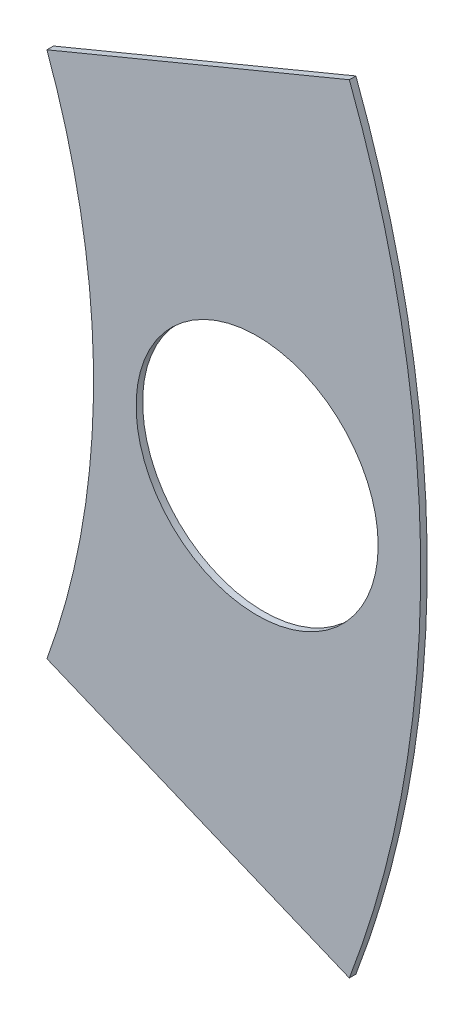
SolidWorks part; units mm, degrees
material "Copper"
ref_plane "Front Plane" through (0, 0, 0) normal (0, 0, 1) x (1, 0, 0)
ref_plane "Top Plane" through (0, 0, 0) normal (0, 1, 0) x (1, 0, 0)
ref_plane "Right Plane" through (0, 0, 0) normal (1, 0, 0) x (0, 0, -1)
sketch "Sketch4" plane through (0, 0, 0) normal (0, 0, 1) x (1, 0, 0)
  circle A0 centre (0, 0) radius 42.545
  dimension "D1" = 85.09
extrude "Boss-Extrude2" add sketch "Sketch4" along normal blind 0.254
sketch "Sketch5" plane through (0, 0, 0.254) normal (0, 0, 1) x (1, 0, 0)
  circle A0 centre (0, 0) radius 29.845
  circle A1 centre (0, 0) radius 42.545 construction
  dimension "D1" = 12.7
extrude "Cut-Extrude5" cut sketch "Sketch5" against normal through all
sketch "Sketch6" plane through (0, 0, 0.254) normal (0, 0, 1) x (1, 0, 0)
  line L0 (0, 0) -> (36.195, 0) construction
  circle A0 centre (36.195, 0) radius 4.699
  circle A1 centre (0, 0) radius 29.845 construction
  dimension "D2" = 9.398
  dimension "D1" = 6.35
extrude "Cut-Extrude6" cut sketch "Sketch6" against normal through all
sketch "Sketch8" plane through (0, 0, 0.254) normal (0, 0, 1) x (1, 0, 0)
  line L0 (0, 0) -> (39.3065, 16.2813) construction
  line L1 (0, 0) -> (39.3065, -16.2813) construction
  line L2 (28.0342, -10.2375) -> (39.7749, -15.1007)
  line L3 (28.0342, 10.2375) -> (39.7749, 15.1007)
  line L6 (0, 0) -> (36.195, 0) construction
  circle A0 centre (0, 0) radius 42.545 construction
  arc A1 (28.0342, -10.2375) -> (28.0342, 10.2375) centre (0, 0) ccw
  circle A2 centre (36.195, 0) radius 4.699 construction
  circle A3 centre (0, 0) radius 29.845 construction
  arc A4 (39.7749, -15.1007) -> (39.7749, 15.1007) centre (0, 0) ccw
  point P26 (0, 0)
  dimension "D4" = 1.27
  dimension "D1" = 22.5
  dimension "D2" = 22.5
  dimension "D5" = 1.27
extrude "Cut-Extrude11" cut sketch "Sketch8" against normal through all flip side to cut
